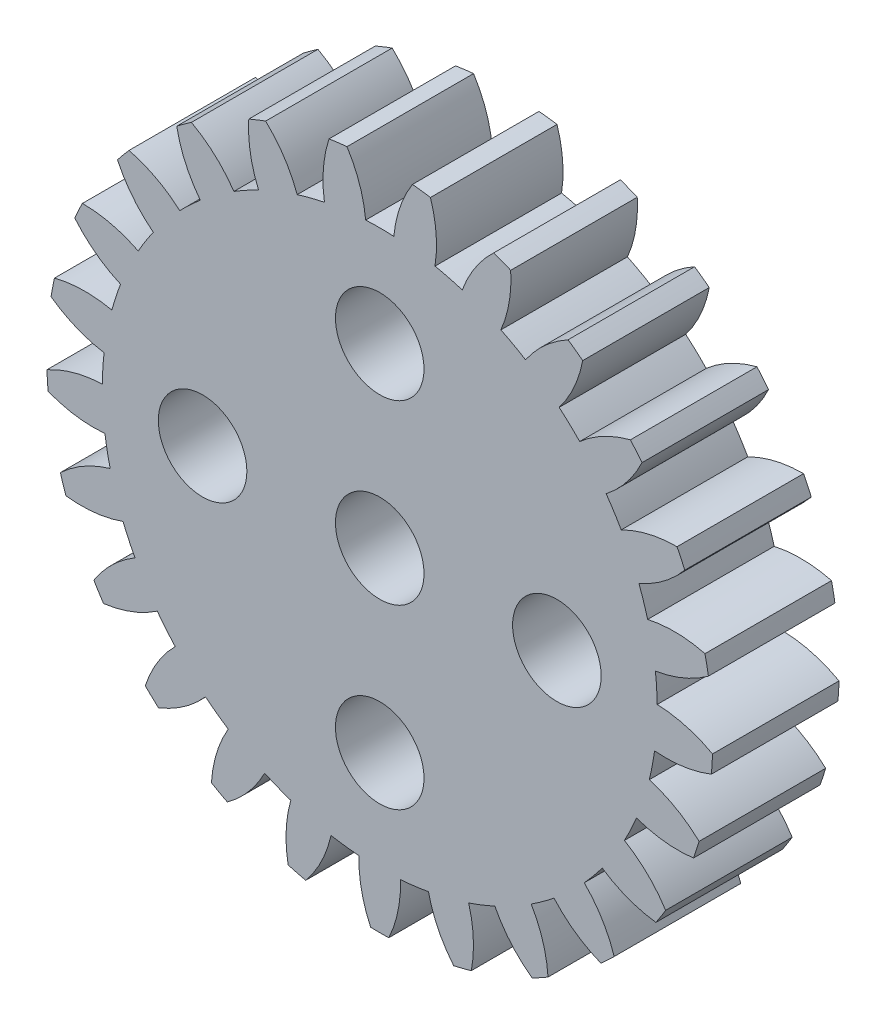
SolidWorks part; units mm, degrees
ref_plane "前视基准面" through (0, 0, 0) normal (0, 0, 1) x (1, 0, 0)
ref_plane "上视基准面" through (0, 0, 0) normal (0, 1, 0) x (1, 0, 0)
ref_plane "右视基准面" through (0, 0, 0) normal (1, 0, 0) x (0, 0, -1)
sketch "草图1" plane through (0, 0, 0) normal (0, 0, 1) x (1, 0, 0)
  arc A0 (-33.6263, 34.8003) -> (-31.5325, 33.9308) centre (-30.7618, 38.7424) ccw
  arc A1 (-31.5325, 33.9308) -> (-31.6023, 32.8203) centre (-20.6398, 32.688) ccw
  arc A2 (-31.6023, 32.8203) -> (-33.7886, 32.2201) centre (-31.4408, 27.95) ccw
  arc A3 (-33.7886, 32.2201) -> (-33.7436, 31.5043) centre (-20.6398, 32.688) ccw
  arc A4 (-33.7436, 31.5043) -> (-31.4993, 31.1828) centre (-31.9494, 36.035) ccw
  arc A5 (-31.4993, 31.1828) -> (-31.2908, 30.0899) centre (-20.6398, 32.688) ccw
  arc A6 (-31.2908, 30.0899) -> (-33.2592, 28.9648) centre (-29.9231, 25.4127) ccw
  arc A7 (-33.2592, 28.9648) -> (-33.0375, 28.2827) centre (-20.6398, 32.688) ccw
  arc A8 (-33.0375, 28.2827) -> (-30.7838, 28.5295) centre (-32.4265, 33.1173) ccw
  arc A9 (-30.7838, 28.5295) -> (-30.3101, 27.5227) centre (-20.6398, 32.688) ccw
  arc A10 (-30.3101, 27.5227) -> (-31.9368, 25.9435) centre (-27.8222, 23.3326) ccw
  arc A11 (-31.9368, 25.9435) -> (-31.5525, 25.3379) centre (-20.6398, 32.688) ccw
  arc A12 (-31.5525, 25.3379) -> (-29.4309, 26.1374) centre (-32.1629, 30.1725) ccw
  arc A13 (-29.4309, 26.1374) -> (-28.7217, 25.2801) centre (-20.6398, 32.688) ccw
  arc A14 (-28.7217, 25.2801) -> (-29.9046, 23.3459) centre (-25.27, 21.8404) ccw
  arc A15 (-29.9046, 23.3459) -> (-29.3817, 22.855) centre (-20.6398, 32.688) ccw
  arc A16 (-29.3817, 22.855) -> (-27.5256, 24.1569) centre (-31.1753, 27.3859) ccw
  arc A17 (-27.5256, 24.1569) -> (-26.6255, 23.503) centre (-20.6398, 32.688) ccw
  arc A18 (-26.6255, 23.503) -> (-27.2902, 21.3354) centre (-22.4268, 21.0297) ccw
  arc A19 (-27.2902, 21.3354) -> (-26.6617, 20.9899) centre (-20.6398, 32.688) ccw
  arc A20 (-26.6617, 20.9899) -> (-25.1877, 22.7125) centre (-29.5257, 24.9324) ccw
  arc A21 (-25.1877, 22.7125) -> (-24.1532, 22.3029) centre (-20.6398, 32.688) ccw
  arc A22 (-24.1532, 22.3029) -> (-24.258, 20.0382) centre (-19.4713, 20.9516) ccw
  arc A23 (-24.258, 20.0382) -> (-23.5633, 19.8598) centre (-20.6398, 32.688) ccw
  arc A24 (-23.5633, 19.8598) -> (-22.564, 21.8949) centre (-27.3178, 22.9662) ccw
  arc A25 (-22.564, 21.8949) -> (-21.4602, 21.7555) centre (-20.6398, 32.688) ccw
  arc A26 (-21.4602, 21.7555) -> (-20.9984, 19.5358) centre (-16.5893, 21.6109) ccw
  arc A27 (-20.9984, 19.5358) -> (-20.2812, 19.5358) centre (-20.6398, 32.688) ccw
  arc A28 (-20.2812, 19.5358) -> (-19.8194, 21.7555) centre (-24.6903, 21.6109) ccw
  arc A29 (-19.8194, 21.7555) -> (-18.7156, 21.8949) centre (-20.6398, 32.688) ccw
  arc A30 (-18.7156, 21.8949) -> (-17.7163, 19.8598) centre (-13.9618, 22.9662) ccw
  arc A31 (-17.7163, 19.8598) -> (-17.0216, 20.0382) centre (-20.6398, 32.688) ccw
  arc A32 (-17.0216, 20.0382) -> (-17.1264, 22.3029) centre (-21.8083, 20.9516) ccw
  arc A33 (-17.1264, 22.3029) -> (-16.0919, 22.7125) centre (-20.6398, 32.688) ccw
  arc A34 (-16.0919, 22.7125) -> (-14.6179, 20.9899) centre (-11.7538, 24.9324) ccw
  arc A35 (-14.6179, 20.9899) -> (-13.9894, 21.3354) centre (-20.6398, 32.688) ccw
  arc A36 (-13.9894, 21.3354) -> (-14.6541, 23.503) centre (-18.8528, 21.0297) ccw
  arc A37 (-14.6541, 23.503) -> (-13.754, 24.1569) centre (-20.6398, 32.688) ccw
  arc A38 (-13.754, 24.1569) -> (-11.8979, 22.855) centre (-10.1043, 27.3859) ccw
  arc A39 (-11.8979, 22.855) -> (-11.375, 23.3459) centre (-20.6398, 32.688) ccw
  arc A40 (-11.375, 23.3459) -> (-12.5579, 25.2801) centre (-16.0096, 21.8404) ccw
  arc A41 (-12.5579, 25.2801) -> (-11.8487, 26.1374) centre (-20.6398, 32.688) ccw
  arc A42 (-11.8487, 26.1374) -> (-9.7271, 25.3379) centre (-9.1167, 30.1725) ccw
  arc A43 (-9.7271, 25.3379) -> (-9.3428, 25.9435) centre (-20.6398, 32.688) ccw
  arc A44 (-9.3428, 25.9435) -> (-10.9695, 27.5227) centre (-13.4574, 23.3326) ccw
  arc A45 (-10.9695, 27.5227) -> (-10.4958, 28.5295) centre (-20.6398, 32.688) ccw
  arc A46 (-10.4958, 28.5295) -> (-8.2421, 28.2827) centre (-8.8531, 33.1173) ccw
  arc A47 (-8.2421, 28.2827) -> (-8.0204, 28.9648) centre (-20.6398, 32.688) ccw
  arc A48 (-8.0204, 28.9648) -> (-9.9888, 30.0899) centre (-11.3565, 25.4127) ccw
  arc A49 (-9.9888, 30.0899) -> (-9.7803, 31.1828) centre (-20.6398, 32.688) ccw
  arc A50 (-9.7803, 31.1828) -> (-7.536, 31.5043) centre (-9.3302, 36.035) ccw
  arc A51 (-7.536, 31.5043) -> (-7.491, 32.2201) centre (-20.6398, 32.688) ccw
  arc A52 (-7.491, 32.2201) -> (-9.6773, 32.8203) centre (-9.8388, 27.95) ccw
  arc A53 (-9.6773, 32.8203) -> (-9.7471, 33.9308) centre (-20.6398, 32.688) ccw
  arc A54 (-9.7471, 33.9308) -> (-7.6533, 34.8003) centre (-10.5178, 38.7424) ccw
  arc A55 (-7.6533, 34.8003) -> (-7.7877, 35.5048) centre (-20.6398, 32.688) ccw
  arc A56 (-7.7877, 35.5048) -> (-10.0546, 35.5424) centre (-8.9998, 30.7849) ccw
  arc A57 (-10.0546, 35.5424) -> (-10.3984, 36.6006) centre (-20.6398, 32.688) ccw
  arc A58 (-10.3984, 36.6006) -> (-8.5866, 37.9635) centre (-12.3415, 41.0695) ccw
  arc A59 (-8.5866, 37.9635) -> (-8.892, 38.6125) centre (-20.6398, 32.688) ccw
  arc A60 (-8.892, 38.6125) -> (-11.097, 38.0852) centre (-8.8923, 33.7395) ccw
  arc A61 (-11.097, 38.0852) -> (-11.6932, 39.0246) centre (-20.6398, 32.688) ccw
  arc A62 (-11.6932, 39.0246) -> (-10.2772, 40.7953) centre (-14.6866, 42.8699) ccw
  arc A63 (-10.2772, 40.7953) -> (-10.7344, 41.3479) centre (-20.6398, 32.688) ccw
  arc A64 (-10.7344, 41.3479) -> (-12.739, 40.2888) centre (-9.5228, 36.6279) ccw
  arc A65 (-12.739, 40.2888) -> (-13.5501, 41.0505) centre (-20.6398, 32.688) ccw
  arc A66 (-13.5501, 41.0505) -> (-12.619, 43.1176) centre (-17.4057, 44.0305) ccw
  arc A67 (-12.619, 43.1176) -> (-13.1992, 43.5392) centre (-20.6398, 32.688) ccw
  arc A68 (-13.1992, 43.5392) -> (-14.8775, 42.0149) centre (-10.8519, 39.2688) ccw
  arc A69 (-14.8775, 42.0149) -> (-15.8525, 42.5509) centre (-20.6398, 32.688) ccw
  arc A70 (-15.8525, 42.5509) -> (-15.4647, 44.7847) centre (-20.3281, 44.4784) ccw
  arc A71 (-15.4647, 44.7847) -> (-16.1316, 45.0487) centre (-20.6398, 32.688) ccw
  arc A72 (-16.1316, 45.0487) -> (-17.378, 43.1549) centre (-12.796, 41.4962) ccw
  arc A73 (-17.378, 43.1549) -> (-18.4557, 43.4316) centre (-20.6398, 32.688) ccw
  arc A74 (-18.4557, 43.4316) -> (-18.6356, 45.6916) centre (-23.27, 44.1855) ccw
  arc A75 (-18.6356, 45.6916) -> (-19.3472, 45.7815) centre (-20.6398, 32.688) ccw
  arc A76 (-19.3472, 45.7815) -> (-20.0835, 43.6372) centre (-15.2329, 43.1702) ccw
  arc A77 (-20.0835, 43.6372) -> (-21.1961, 43.6372) centre (-20.6398, 32.688) ccw
  arc A78 (-21.1961, 43.6372) -> (-21.9324, 45.7815) centre (-26.0467, 43.1702) ccw
  arc A79 (-21.9324, 45.7815) -> (-22.644, 45.6916) centre (-20.6398, 32.688) ccw
  arc A80 (-22.644, 45.6916) -> (-22.8239, 43.4316) centre (-18.0096, 44.1855) ccw
  arc A81 (-22.8239, 43.4316) -> (-23.9016, 43.1549) centre (-20.6398, 32.688) ccw
  arc A82 (-23.9016, 43.1549) -> (-25.148, 45.0487) centre (-28.4836, 41.4962) ccw
  arc A83 (-25.148, 45.0487) -> (-25.8149, 44.7847) centre (-20.6398, 32.688) ccw
  arc A84 (-25.8149, 44.7847) -> (-25.4271, 42.5509) centre (-20.9515, 44.4784) ccw
  arc A85 (-25.4271, 42.5509) -> (-26.4021, 42.0149) centre (-20.6398, 32.688) ccw
  arc A86 (-26.4021, 42.0149) -> (-28.0804, 43.5392) centre (-30.4277, 39.2688) ccw
  arc A87 (-28.0804, 43.5392) -> (-28.6606, 43.1176) centre (-20.6398, 32.688) ccw
  arc A88 (-28.6606, 43.1176) -> (-27.7295, 41.0505) centre (-23.8739, 44.0305) ccw
  arc A89 (-27.7295, 41.0505) -> (-28.5406, 40.2888) centre (-20.6398, 32.688) ccw
  arc A90 (-28.5406, 40.2888) -> (-30.5452, 41.3479) centre (-31.7568, 36.6279) ccw
  arc A91 (-30.5452, 41.3479) -> (-31.0024, 40.7953) centre (-20.6398, 32.688) ccw
  arc A92 (-31.0024, 40.7953) -> (-29.5864, 39.0246) centre (-26.593, 42.8699) ccw
  arc A93 (-29.5864, 39.0246) -> (-30.1826, 38.0852) centre (-20.6398, 32.688) ccw
  arc A94 (-30.1826, 38.0852) -> (-32.3876, 38.6125) centre (-32.3873, 33.7395) ccw
  arc A95 (-32.3876, 38.6125) -> (-32.693, 37.9635) centre (-20.6398, 32.688) ccw
  arc A96 (-32.693, 37.9635) -> (-30.8812, 36.6006) centre (-28.9381, 41.0695) ccw
  arc A97 (-30.8812, 36.6006) -> (-31.225, 35.5424) centre (-20.6398, 32.688) ccw
  arc A98 (-31.225, 35.5424) -> (-33.4919, 35.5048) centre (-32.2798, 30.7849) ccw
  arc A99 (-33.4919, 35.5048) -> (-33.6263, 34.8003) centre (-20.6398, 32.688) ccw
  circle A100 centre (-20.6398, 32.688) radius 7 construction
  circle A101 centre (-20.6398, 39.688) radius 1.75
  circle A102 centre (-13.6398, 32.688) radius 1.75
  circle A103 centre (-20.6398, 25.688) radius 1.75
  circle A104 centre (-27.6398, 32.688) radius 1.75
  circle A105 centre (-20.6398, 32.688) radius 1.75
  point P212 (-20.6398, 32.688)
  dimension "D1" = 14
  dimension "D2" = 3.5
  dimension "D4" = 3.5
  dimension "D3" = 4
extrude "凸台-拉伸1" add sketch "草图1" along normal blind 5
